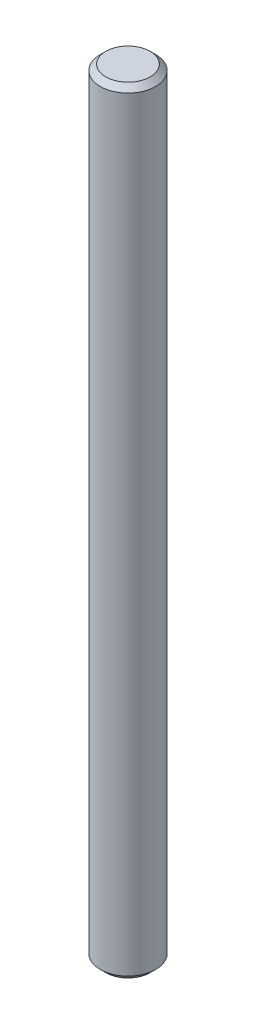
SolidWorks part; units mm, degrees
material "1.6523 (20NiCrMoS2-2)"
ref_plane "Front Plane" through (0, 0, 0) normal (0, 0, 1) x (1, 0, 0)
ref_plane "Top Plane" through (0, 0, 0) normal (0, 1, 0) x (1, 0, 0)
ref_plane "Right Plane" through (0, 0, 0) normal (1, 0, 0) x (0, 0, -1)
sketch "Sketch1" plane through (0, 0, 0) normal (0, 1, 0) x (1, 0, 0)
  circle A0 centre (0, 0) radius 2.5
  dimension "D1" = 5
extrude "Boss-Extrude1" add sketch "Sketch1" along normal blind 70
chamfer "Chamfer1" distance 0.5 angle 45 2 edges at (0, 0, 2.5) (0, 70, 2.5)
